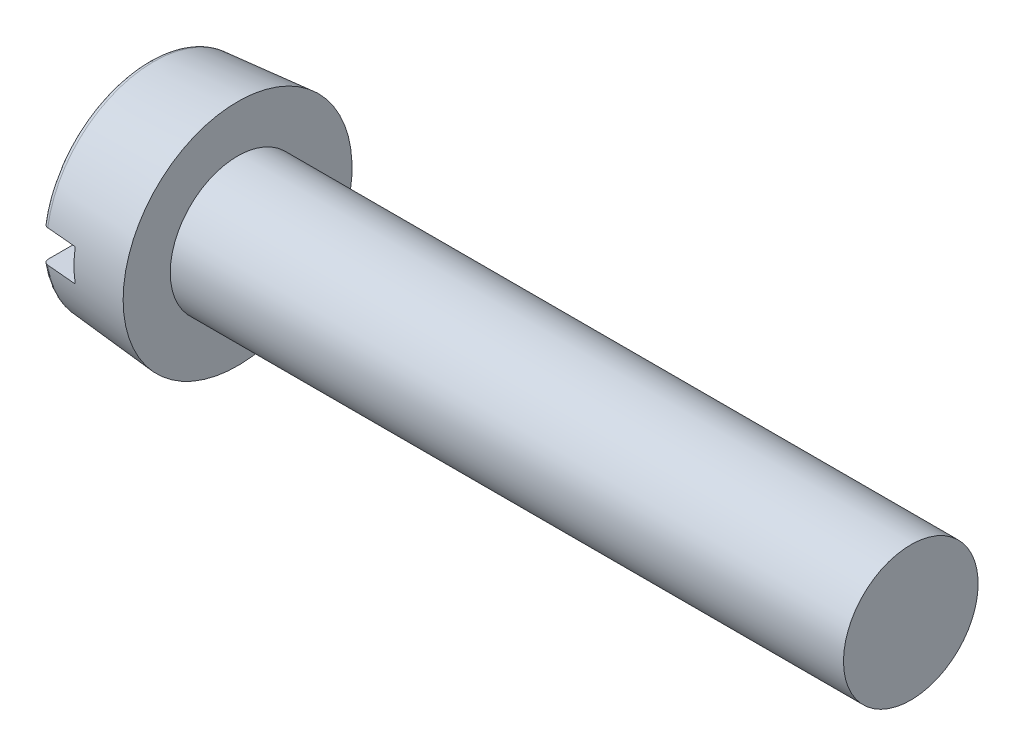
SolidWorks part; units mm, degrees
ref_plane "Plane1" through (0, 0, 0) normal (0, 0, 1) x (1, 0, 0)
ref_plane "Plane2" through (0, 0, 0) normal (0, 1, 0) x (1, 0, 0)
ref_plane "Plane3" through (0, 0, 0) normal (1, 0, 0) x (0, 0, -1)
sketch "BodySke" plane through (0, 0, 0) normal (0, 0, 1) x (1, 0, 0)
  line L0 (3.3, 2.5) -> (3.3, 4.25)
  line L1 (0, 0) -> (0, 3.9613)
  line L2 (-25.4, 0) -> (127, 0) construction
  line L3 (28.3, 0) -> (0, 0)
  line L4 (3.3, 2.5) -> (28.3, 2.5)
  line L5 (28.3, 2.5) -> (28.3, 0)
  line L6 (0, 3.9613) -> (3.3, 4.25)
  line L9 (4.1, 4.0875) -> (4.1, -5.4375) construction
  line L10 (3.3, 6.35) -> (3.3, -3.175) construction
  dimension "Length" = 25
  dimension "Head_ht" = 3.3
  dimension "Advance" = 0.8
  dimension "Thread_nom" = 25
  dimension "Head_dia" = 8.5
  dimension "Head_side_angle" = 5
  dimension "Diameter" = 5
revolve "Base-Revolve" add sketch "BodySke"
cosmetic thread "ThreadCosmetic"
fillet "Fillet1" [suppressed] radius 0.2
fillet "Fillet2" radius 0.2 1 edges at (0, 0, 3.9613)
sketch "Sketch2" plane through (0, 0, 0) normal (1, 0, 0) x (0, 0, -1)
  line L0 (4.25, -0.6) -> (-4.25, -0.6)
  line L1 (4.25, -0.6) -> (4.25, 0.6)
  line L2 (-4.25, 0.6) -> (4.25, 0.6)
  line L3 (-4.25, 0.6) -> (-4.25, -0.6)
  dimension "D1" = 8.5
  dimension "Slot_width" = 1.2
  dimension "D2" = 4.25
  dimension "D3" = 0.6
extrude "Slot" cut sketch "Sketch2" along normal blind 1.3
sketch "ThdSchSke" plane through (0, 0, 0) normal (0, 0, 1) x (1, 0, 0)
  line L0 (4.9, -2.055) -> (4.5884, -2.5)
  line L1 (4.9, -2.055) -> (5.2116, -2.5)
  line L2 (5.2116, -2.5) -> (5.2116, -3.125)
  line L3 (-3.175, 0) -> (5.1513, 0) construction
  line L5 (5.2116, -3.125) -> (4.5884, -3.125)
  line L6 (4.5884, -3.125) -> (4.5884, -2.5)
  dimension "Diameter" = 5
  dimension "SideAngle" = 55
  dimension "VeeAngle" = 70
  dimension "Thread_minor" = 4.11
  dimension "Overcut" = 6.25
  dimension "Start" = 4.9
revolve "ThreadSchematic" [suppressed] cut sketch "ThdSchSke" angle 360 about L3
pattern_linear "ThdSchPat" [suppressed]
equation "\"D1@Sketch2\" = \"Head_dia@BodySke\""
equation "\"D2@Sketch2\" = \"D1@Sketch2\" / 2"
equation "\"D3@Sketch2\" = \"Slot_width@Sketch2\" / 2"
equation "\"Thread_length@ThreadCosmetic\" = ((sgn( (\"Length@BodySke\" - \"Advance@BodySke\" * 2.0 ) - \"Thread_nom@BodySke\" )-1)*( (\"Length@BodySke\" - \"Advance@BodySke\"  * 2.0) - \"Thread_nom@BodySke\" ))/-2+ \"Thread_nom@BodySke\""
equation "\"Thread_minor@ThdSchSke\" = \"Thread_minor@ThreadCosmetic\""
equation "\"Diameter@ThdSchSke\" = \"Diameter@BodySke\""
equation "\"Overcut@ThdSchSke\" = \"Diameter@BodySke\" * 1.25"
equation "\"Start@ThdSchSke\" = \"Head_ht@BodySke\" + \"Length@BodySke\" - \"Thread_length@ThreadCosmetic\"  '---Non-countersunk---"
equation "\"Num_threads@ThdSchPat\" = int( \"Thread_length@ThreadCosmetic\" / \"Advance@BodySke\" + 0.999 )  + 1"
equation "\"Advance@ThdSchPat\" = \"Thread_length@ThreadCosmetic\" /  (\"Num_threads@ThdSchPat\" - 1) 'relax it"
